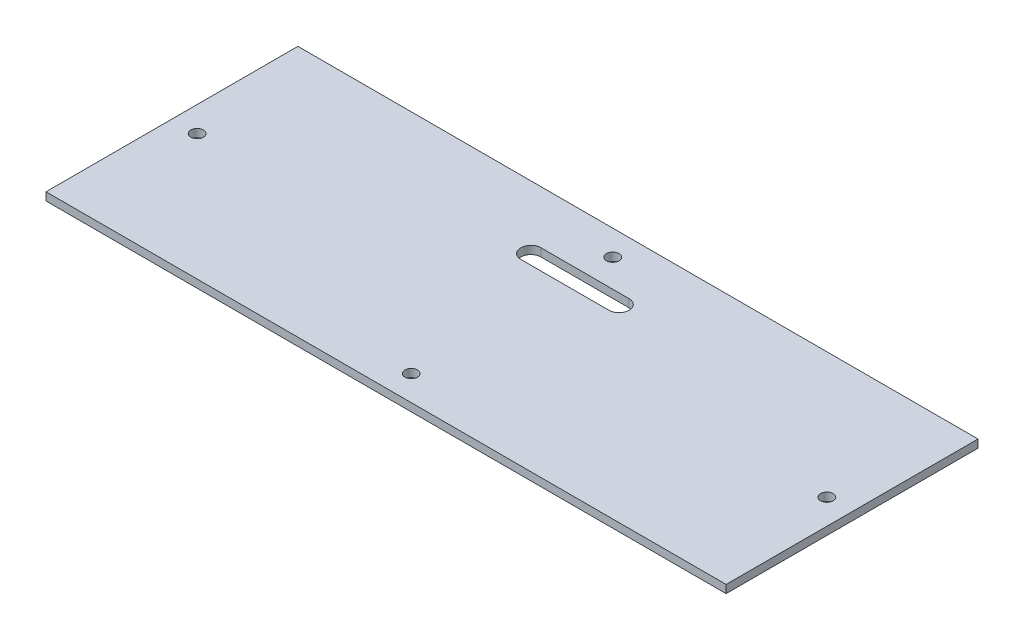
SolidWorks part; units mm, degrees
ref_plane "Front Plane" through (0, 0, 0) normal (0, 0, 1) x (1, 0, 0)
ref_plane "Top Plane" through (0, 0, 0) normal (0, 1, 0) x (1, 0, 0)
ref_plane "Right Plane" through (0, 0, 0) normal (1, 0, 0) x (0, 0, -1)
sketch "Sketch1" plane through (0, 0, 0) normal (0, 1, 0) x (1, 0, 0)
  line L1 (0, 0) -> (270, 0)
  line L2 (0, 0) -> (0, 100)
  line L3 (0, 100) -> (270, 100)
  line L4 (270, 0) -> (270, 100)
  line L5 (0, 105) -> (270, 105)
  line L6 (0, 105) -> (0, 245)
  line L7 (0, 245) -> (270, 245)
  line L8 (270, 105) -> (270, 245)
  dimension "D1" = 140
  dimension "D2" = 100
  dimension "D3" = 270
  dimension "D4" = 270
  dimension "D5" = 5
extrude "Boss-Extrude1" add sketch "Sketch1" along normal blind 3.175
sketch "Sketch2" plane through (0, 3.175, 0) normal (0, 1, 0) x (1, 0, 0)
  line L0 (0, 245) -> (0, 105) construction
  line L1 (270, 245) -> (0, 245) construction
  line L2 (270, 105) -> (270, 245) construction
  line L3 (0, 105) -> (270, 105) construction
  line L4 (270, 100) -> (0, 100) construction
  line L5 (0, 100) -> (0, 0) construction
  line L6 (0, 0) -> (270, 0) construction
  line L7 (270, 0) -> (270, 100) construction
  line L8 (117.5, 75) -> (152.5, 75) construction
  line L9 (117.5, 79) -> (152.5, 79)
  line L10 (117.5, 71) -> (152.5, 71)
  circle A0 centre (10, 175) radius 2.5
  circle A1 centre (10, 50) radius 2.5
  circle A2 centre (260, 50) radius 2.5
  circle A3 centre (260, 175) radius 2.5
  circle A4 centre (135, 115) radius 2.5
  circle A5 centre (135, 235) radius 2.5
  circle A6 centre (135, 90) radius 2.5
  circle A7 centre (135, 10) radius 2.5
  arc A8 (117.5, 79) -> (117.5, 71) centre (117.5, 75) ccw
  arc A9 (152.5, 71) -> (152.5, 79) centre (152.5, 75) ccw
  point P33 (0, 50)
  point P35 (135, 0)
  point P36 (135, 75)
  point P37 (270, 50)
  point P39 (135, 100)
  point P41 (135, 105)
  point P43 (135, 245)
  point P45 (0, 175)
  point P46 (0, 0)
  point P47 (270, 175)
  point P48 (120.4334, 66.4602)
  dimension "D1" = 5
  dimension "D2" = 10
  dimension "D3" = 10
  dimension "D4" = 10
  dimension "D5" = 10
  dimension "D6" = 10
  dimension "D7" = 10
  dimension "D8" = 10
  dimension "D9" = 10
  dimension "D10" = 8
  dimension "D11" = 25
  dimension "D12" = 35
extrude "Cut-Extrude1" cut sketch "Sketch2" against normal through all both and the other way through all
delete or keep bodies "Body-Delete/Keep 1" type delete bodies bodies 104
